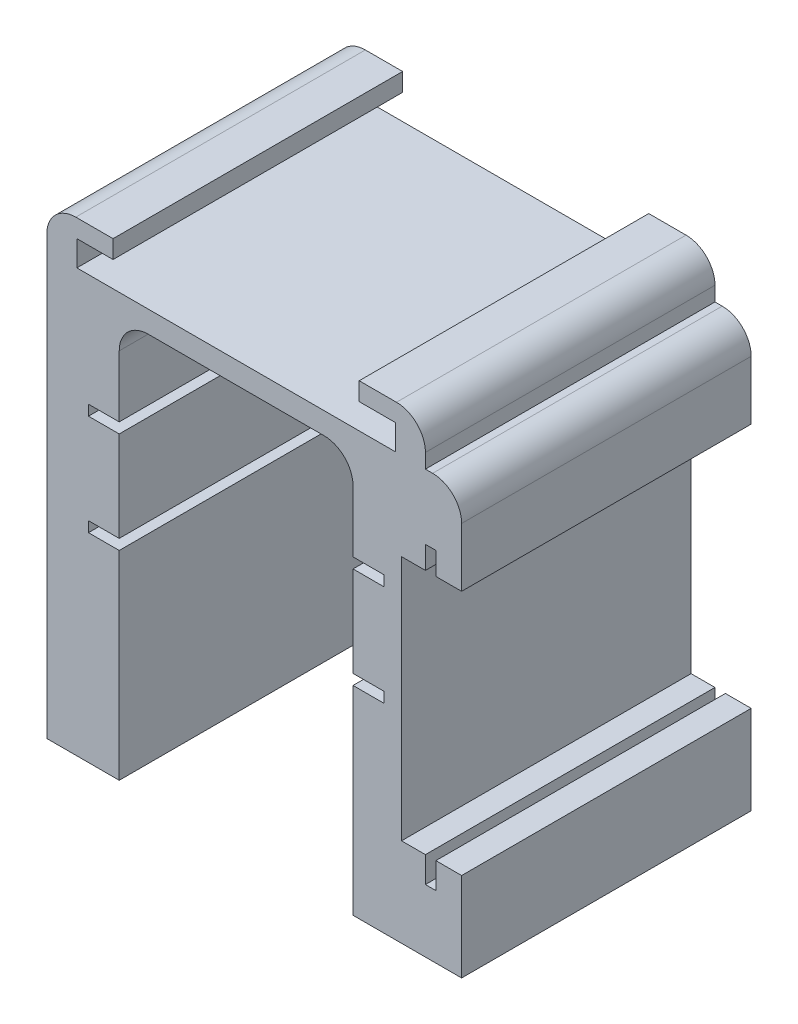
SolidWorks part; units mm, degrees
ref_plane "Front Plane" through (0, 0, 0) normal (0, 0, 1) x (1, 0, 0)
ref_plane "Top Plane" through (0, 0, 0) normal (0, 1, 0) x (1, 0, 0)
ref_plane "Right Plane" through (0, 0, 0) normal (1, 0, 0) x (0, 0, -1)
sketch "Sketch1" plane through (0, 0, 0) normal (0, 0, 1) x (1, 0, 0)
  line L1 (12.7, 70.3326) -> (12.7, 54.4576)
  line L2 (12.7, 54.4576) -> (7.3025, 54.4576)
  line L3 (7.3025, 54.4576) -> (7.3025, 52.6288)
  line L4 (7.3025, 52.6288) -> (12.7, 52.6288)
  line L5 (12.7, 52.6288) -> (12.7, 36.7538)
  line L6 (12.7, 36.7538) -> (7.3025, 36.7538)
  line L7 (7.3025, 36.7538) -> (7.3025, 34.925)
  line L8 (7.3025, 34.925) -> (12.7, 34.925)
  line L9 (12.7, 34.925) -> (12.7, 0)
  line L10 (12.7, 0) -> (0, 0)
  line L11 (0, 0) -> (0, 74.1426)
  line L13 (12.7, 70.3326) -> (53.721, 70.3326)
  line L15 (0, 74.1426) -> (66.421, 74.1426)
  line L16 (33.2105, 70.3326) -> (33.2105, 74.1426) construction
  line L17 (66.421, 11.0236) -> (66.421, 62.7126)
  line L18 (53.721, 0) -> (66.421, 0)
  line L19 (53.721, 34.925) -> (53.721, 0)
  line L20 (59.1185, 34.925) -> (53.721, 34.925)
  line L21 (59.1185, 36.7538) -> (59.1185, 34.925)
  line L22 (53.721, 36.7538) -> (59.1185, 36.7538)
  line L23 (53.721, 52.6288) -> (53.721, 36.7538)
  line L24 (59.1185, 52.6288) -> (53.721, 52.6288)
  line L25 (59.1185, 54.4576) -> (59.1185, 52.6288)
  line L26 (53.721, 54.4576) -> (59.1185, 54.4576)
  line L27 (53.721, 70.3326) -> (53.721, 54.4576)
  line L29 (66.421, 74.1426) -> (72.771, 74.1426)
  line L30 (66.421, 62.7126) -> (66.421, 11.0236)
  line L31 (66.421, 0) -> (72.771, 0)
  line L32 (72.771, 74.1426) -> (72.771, 58.7526)
  line L33 (68.2498, 58.7526) -> (65.151, 58.7526) construction
  line L34 (72.771, 58.7526) -> (68.2498, 58.7526)
  line L35 (72.771, 58.7526) -> (72.771, 15.5726) construction
  line L36 (72.771, 15.5726) -> (68.2498, 15.5726)
  line L38 (66.421, 62.7126) -> (68.2498, 62.7126)
  line L39 (66.421, 62.7126) -> (66.421, 11.0236)
  line L40 (66.421, 11.0236) -> (68.2498, 11.0236)
  line L41 (68.2498, 62.7126) -> (68.2498, 58.7526)
  line L42 (72.771, 58.7526) -> (72.771, 15.5726) construction
  line L43 (72.771, 15.5726) -> (72.771, 0)
  line L44 (68.2498, 58.7526) -> (68.2498, 15.5726) construction
  line L45 (68.2498, 15.5726) -> (68.2498, 11.0236)
  line L47 (66.421, 62.7126) -> (66.421, 74.1426) construction
  line L48 (66.421, 74.1426) -> (66.421, 62.7126) construction
  line L49 (66.421, 0) -> (66.421, 11.0236) construction
  line L50 (66.421, 11.0236) -> (66.421, 0) construction
  line L51 (33.2105, -926.1114) -> (33.2105, 49073.8886) construction
  line L52 (0, 74.1426) -> (5.2705, 74.1426)
  line L53 (0, 74.1426) -> (0, 81.7626)
  line L54 (0, 81.7626) -> (5.2705, 81.7626)
  line L55 (5.2705, 74.1426) -> (5.2705, 78.5876)
  line L56 (5.2705, 81.7626) -> (11.6205, 81.7626)
  line L57 (5.2705, 81.7626) -> (5.2705, 78.5876) construction
  line L58 (5.2705, 78.5876) -> (11.6205, 78.5876)
  line L59 (11.6205, 81.7626) -> (11.6205, 78.5876)
  line L60 (5.2705, 78.5876) -> (5.2705, 81.7626) construction
  line L61 (61.1505, 74.1426) -> (61.1505, 78.5876)
  line L62 (61.1505, 78.5876) -> (54.8005, 78.5876)
  line L63 (66.421, 74.1426) -> (66.421, 81.7626)
  line L64 (66.421, 81.7626) -> (61.1505, 81.7626)
  line L65 (61.1505, 81.7626) -> (54.8005, 81.7626)
  line L66 (54.8005, 81.7626) -> (54.8005, 78.5876)
  line L70 (66.421, 58.7526) -> (62.23, 58.7526)
  line L71 (66.421, 58.7526) -> (66.421, 15.5726)
  line L72 (66.421, 15.5726) -> (62.23, 15.5726)
  line L73 (62.23, 58.7526) -> (62.23, 15.5726)
  point P57 (0, 0)
  point P58 (0, 0)
  point P59 (46.3286, 15.5726)
  dimension "D1" = 1.8288
  dimension "D2" = 1.8288
  dimension "D3" = 5.3975
  dimension "D4" = 12.7
  dimension "D5" = 34.925
  dimension "D6" = 15.875
  dimension "D7" = 15.875
  dimension "D8" = 25.908
  dimension "D9" = 3.81
  dimension "D10" = 6.35
  dimension "D12" = 7.62
  dimension "D13" = 51.689
  dimension "D14" = 1.8288
  dimension "D15" = 11.43
  dimension "D16" = 7.62
  dimension "D18" = 6.35
  dimension "D19" = 3.175
  dimension "D17" = 43.18
  dimension "D20" = 4.191
  dimension "D11" = 43.18
extrude "Boss-Extrude1" add sketch "Sketch1" along normal blind 50.8 contours L36 L45 L40 L17 L30 L38 L41 L34 L32 L29 L15 L11 L10 L9 L8 L7 L6 L5 L4 L3 L2 L1 L13 L27 L26 L25 L24 L23 L22 L21 L20 L19 L18 L31 L43 | L59 L56 L54 L53 L15 L55 L58 | L65 L66 L62 L61 L15 L63 L64
sketch "Sketch2" plane through (0, 0, 0) normal (0, -1, 0) x (1, 0, 0)
  line L0 (12.7, 50.8) -> (0, 50.8) construction
  line L2 (0, 50.8) -> (0, 0) construction
  line L3 (72.771, 50.8) -> (72.771, 0) construction
  line L4 (53.721, 0) -> (72.771, 0) construction
  circle A0 centre (6.35, 44.45) radius 2.6035
  circle A1 centre (66.421, 6.35) radius 2.6035
  dimension "D1" = 5.207
  dimension "D4" = 5.207
  dimension "D2" = 6.35
  dimension "D3" = 6.35
  dimension "D5" = 6.35
  dimension "D6" = 6.35
extrude "Cut-Extrude1" cut sketch "Sketch2" against normal blind 5.08
fillet "Fillet1" radius 5.08 5 edges at (72.771, 74.1426, 25.4) (66.421, 81.7626, 25.4) (0, 81.7626, 25.4) (53.721, 70.3326, 25.4) (12.7, 70.3326, 25.4)
equation "\"DUALTB_T\"= 0.062in"
equation "\"TightTol\"= 0.005in"
equation "\"D1@Sketch1\"=\"DUALTB_T\" + 2*\"TightTol\""
equation "\"D2@Sketch1\"=\"DUALTB_T\" + 2*\"TightTol\""
